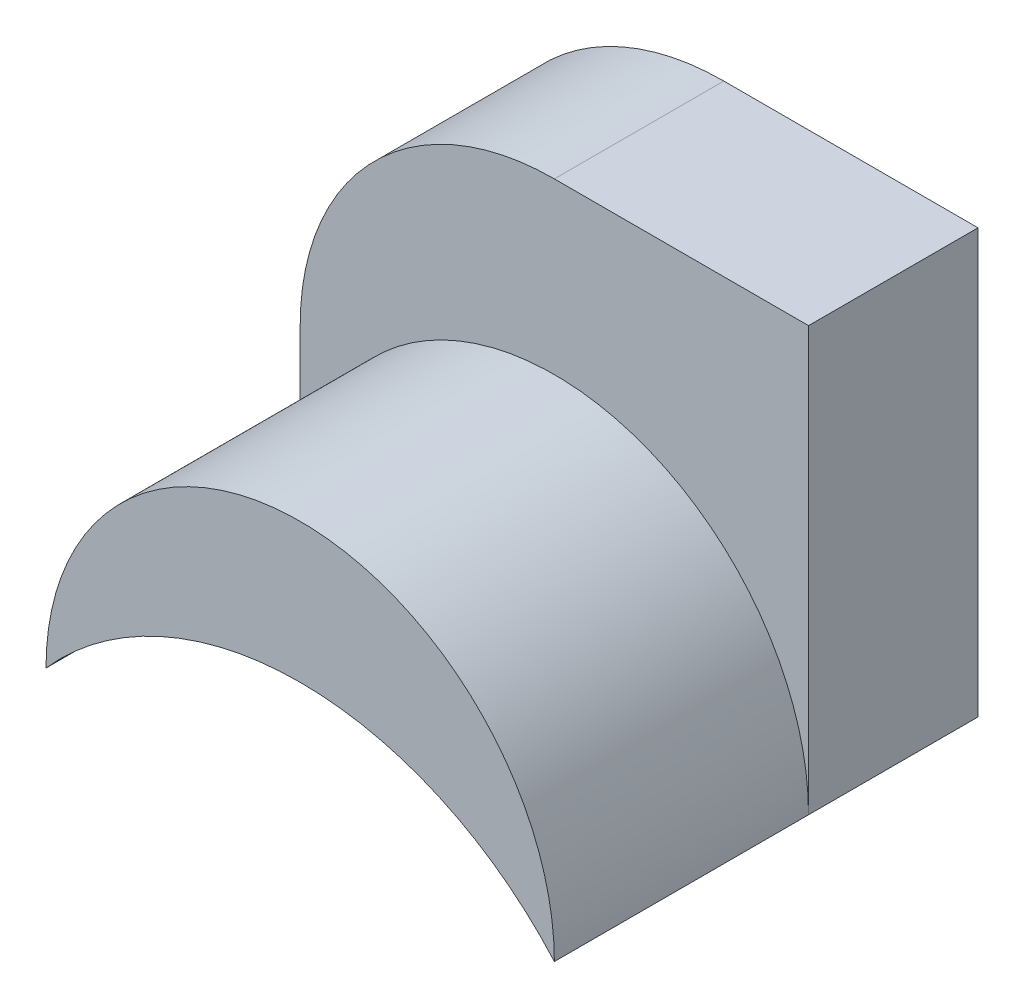
SolidWorks part; units mm, degrees
ref_plane "Front Plane" through (0, 0, 0) normal (0, 0, 1) x (1, 0, 0)
ref_plane "Top Plane" through (0, 0, 0) normal (0, 1, 0) x (1, 0, 0)
ref_plane "Right Plane" through (0, 0, 0) normal (1, 0, 0) x (0, 0, -1)
sketch "Sketch1" plane through (0, 0, 0) normal (0, 0, 1) x (1, 0, 0)
  line L0 (-15, 25) -> (0, 25)
  line L1 (0, 25) -> (0, 0)
  line L2 (0, 0) -> (-30, 0)
  line L3 (-30, 0) -> (-30, 10)
  arc A0 (-30, 10) -> (-15, 25) centre (-15, 10) cw
  dimension "D1" = 15
  dimension "D2" = 10
  dimension "D3" = 25
extrude "Boss-Extrude1" add sketch "Sketch1" along normal blind 10
sketch "Sketch2" plane through (0, 0, 10) normal (0, 0, 1) x (1, 0, 0)
  line L0 (-30, 0) -> (0, 0) construction
  arc A0 (-30, 0) -> (0, 0) centre (-15, 0) cw
  arc A1 (-30, 0) -> (0, 0) centre (-15, -13.2288) cw
  dimension "D1" = 20
extrude "Boss-Extrude2" add sketch "Sketch2" along normal blind 15
